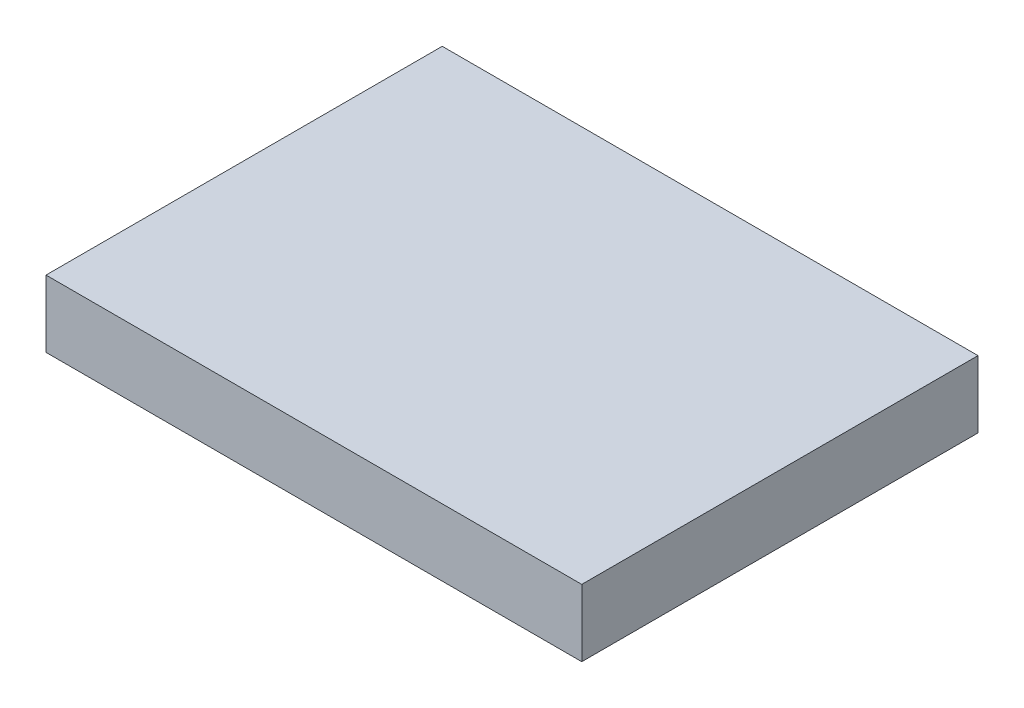
SolidWorks part; units mm, degrees
ref_plane "Plan de face" through (0, 0, 0) normal (0, 0, 1) x (1, 0, 0)
ref_plane "Plan de dessus" through (0, 0, 0) normal (0, 1, 0) x (1, 0, 0)
ref_plane "Plan de droite" through (0, 0, 0) normal (1, 0, 0) x (0, 0, -1)
sketch "Esquisse1" plane through (0, 0, 0) normal (0, 1, 0) x (1, 0, 0)
  line L1 (0, 0) -> (-24, 0)
  line L2 (0, 0) -> (0, 17.75)
  line L3 (0, 17.75) -> (-24, 17.75)
  line L4 (-24, 0) -> (-24, 17.75)
  dimension "D1" = 24
  dimension "D2" = 17.75
extrude "Boss.-Extru.1" add sketch "Esquisse1" along normal blind 3
